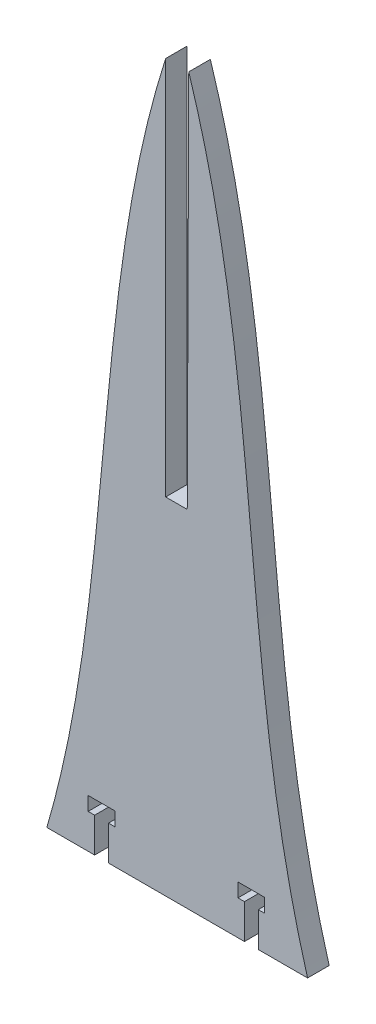
SolidWorks part; units mm, degrees
ref_plane "Front Plane" through (0, 0, 0) normal (0, 0, 1) x (1, 0, 0)
ref_plane "Top Plane" through (0, 0, 0) normal (0, 1, 0) x (1, 0, 0)
ref_plane "Right Plane" through (0, 0, 0) normal (1, 0, 0) x (0, 0, -1)
sketch "Sketch1" plane through (0, 0, 0) normal (0, 0, 1) x (1, 0, 0)
  line L0 (-3.175, 10.16) -> (-3.175, 0) construction
  line L1 (-41.275, 0) -> (-27.2233, 0)
  line L2 (-6.35, 213.232) -> (-6.35, 101.6)
  line L3 (-27.2233, 0) -> (-27.2233, 10.16)
  line L4 (-6.35, 101.6) -> (0, 101.6)
  line L5 (-6.35, 406.4) -> (-6.35, 0) construction
  line L6 (0, 101.6) -> (0.4448, 213.232)
  line L7 (-27.2233, 10.16) -> (-29.1283, 10.16)
  line L8 (-29.1283, 10.16) -> (-29.1283, 14.224)
  line L9 (-29.1283, 14.224) -> (-21.2543, 14.224)
  line L10 (-21.2543, 14.224) -> (-21.2543, 10.16)
  line L11 (-21.2543, 10.16) -> (-23.1593, 10.16)
  line L12 (-23.1593, 10.16) -> (-23.1593, 0)
  line L13 (-23.1593, 0) -> (16.8093, 0)
  line L14 (-6.35, 10.16) -> (0, 10.16) construction
  line L15 (14.9043, 14.224) -> (14.9043, 10.16)
  line L16 (22.7783, 14.224) -> (14.9043, 14.224)
  line L17 (22.7783, 10.16) -> (22.7783, 14.224)
  line L18 (20.8733, 10.16) -> (22.7783, 10.16)
  line L19 (14.9043, 10.16) -> (16.8093, 10.16)
  line L20 (16.8093, 10.16) -> (16.8093, 0)
  line L21 (20.8733, 0) -> (20.8733, 10.16)
  line L22 (20.8733, 0) -> (35.3698, 0)
  spline S0 degree 3 poles (-6.35, 213.232) (-28.5059, 143.7513) (-20.8344, 69.8408) (-41.275, 0) knots 0 0 0 0 1 1 1 1
  spline S1 degree 3 poles (0.4448, 213.232) (22.6008, 143.7513) (14.9293, 69.8408) (35.3698, 0) knots 0 0 0 0 1 1 1 1
extrude "Boss-Extrude1" add sketch "Sketch1" along normal blind 6.35
